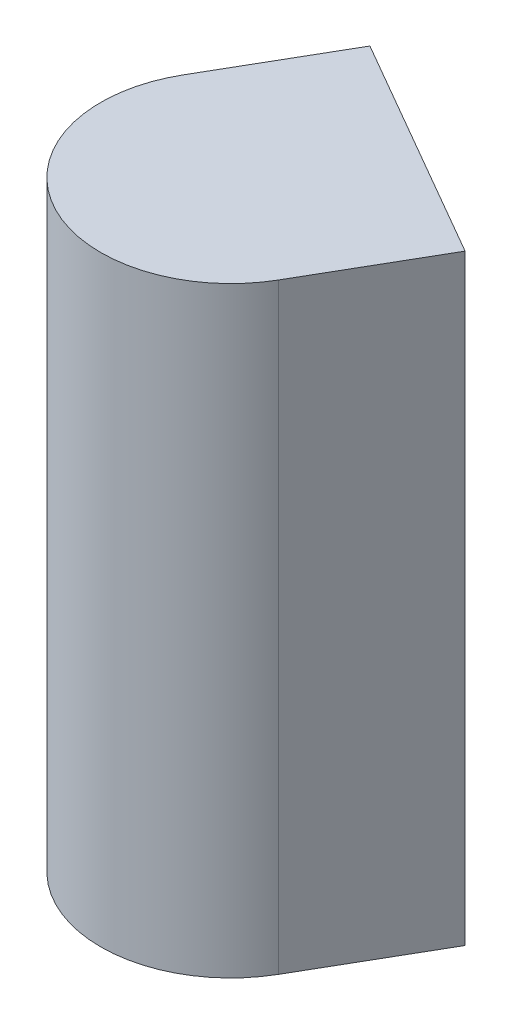
SolidWorks part; units mm, degrees
ref_plane "Front Plane" through (0, 0, 0) normal (0, 0, 1) x (1, 0, 0)
ref_plane "Top Plane" through (0, 0, 0) normal (0, 1, 0) x (1, 0, 0)
ref_plane "Right Plane" through (0, 0, 0) normal (1, 0, 0) x (0, 0, -1)
sketch "Sketch1" plane through (0, 0, 0) normal (0, 1, 0) x (1, 0, 0)
  line L0 (16.1387, -70.5969) -> (14.0359, -74.2391)
  line L1 (23.0669, -74.5969) -> (20.9641, -78.2391)
  line L2 (16.1387, -70.5969) -> (23.0669, -74.5969)
  arc A0 (14.0359, -74.2391) -> (20.9641, -78.2391) centre (17.5, -76.2391) ccw
extrude "Boss-Extrude1" add sketch "Sketch1" along normal blind 18.5
